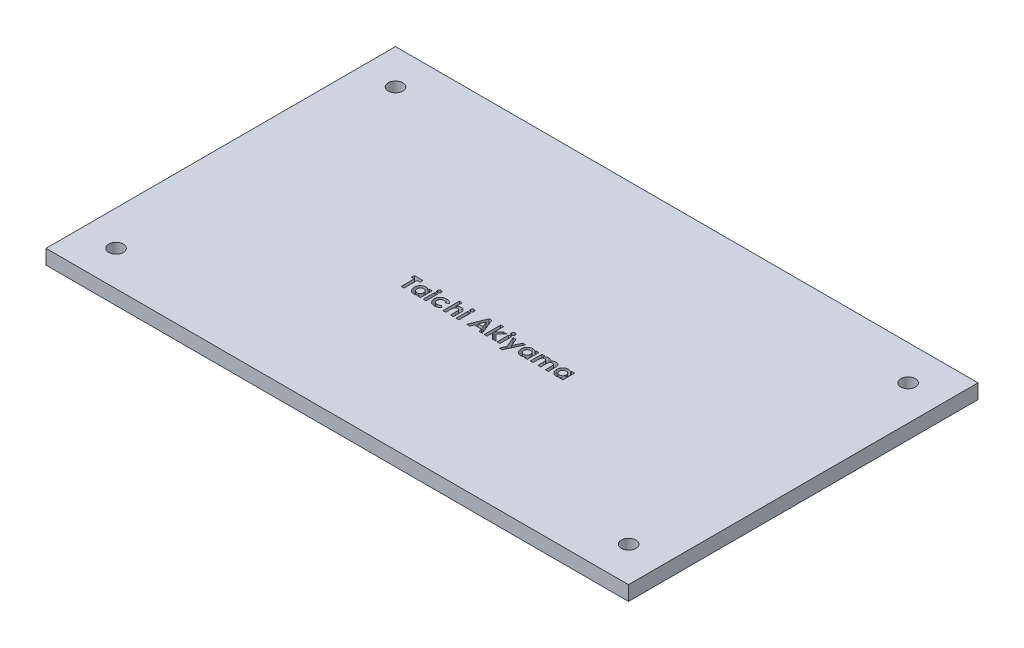
SolidWorks part; units mm, degrees
ref_plane "Front Plane" through (0, 0, 0) normal (0, 0, 1) x (1, 0, 0)
ref_plane "Top Plane" through (0, 0, 0) normal (0, 1, 0) x (1, 0, 0)
ref_plane "Right Plane" through (0, 0, 0) normal (1, 0, 0) x (0, 0, -1)
sketch "Sketch1" plane through (0, 0, 0) normal (0, 1, 0) x (1, 0, 0)
  line L1 (-60.331, 44.6885) -> (66.669, 44.6885)
  line L2 (-60.331, 44.6885) -> (-60.331, -31.5115)
  line L3 (-60.331, -31.5115) -> (66.669, -31.5115)
  line L4 (66.669, 44.6885) -> (66.669, -31.5115)
extrude "Boss-Extrude1" add sketch "Sketch1" along normal blind 3.175
sketch "Sketch2" plane through (0, 0, 0) normal (0, 1, 0) x (1, 0, 0)
  line L0 (-52.711, 52.3085) -> (-52.711, 37.0685) construction
  line L2 (66.669, 44.6885) -> (-60.331, 44.6885) construction
  line L3 (-60.331, 44.6885) -> (-60.331, -31.5115) construction
  line L4 (-52.711, -23.8592) -> (-52.711, -39.0992) construction
  line L5 (59.049, 37.0685) -> (74.289, 37.0685) construction
  line L6 (66.669, -31.5115) -> (66.669, 44.6885) construction
  line L7 (59.049, -23.8592) -> (59.049, -39.0992) construction
  circle A0 centre (-52.711, 37.0685) radius 1.5875
  circle A1 centre (-52.711, -23.8592) radius 1.5875
  circle A2 centre (59.049, 37.0685) radius 1.5875
  circle A3 centre (59.049, -23.8592) radius 1.5875
  point P2 (-52.711, 44.6885)
  point P10 (-52.711, -31.4792)
  point P15 (66.669, 37.0685)
  dimension "D3" = 7.62
  dimension "D4" = 7.62
  dimension "D1" = 7.62
  dimension "D2" = 7.62
extrude "Cut-Extrude1" cut sketch "Sketch2" along normal blind 3.175
sketch "Sketch3" plane through (0, 3.175, 0) normal (0, 1, 0) x (1, 0, 0)
  line L0 (-31.9275, 0) -> (37.4143, 0) construction
  text T0 "<b>Taichi Akiyama</b>"
extrude "Cut-Extrude2" cut sketch "Sketch3" against normal blind 2.54
